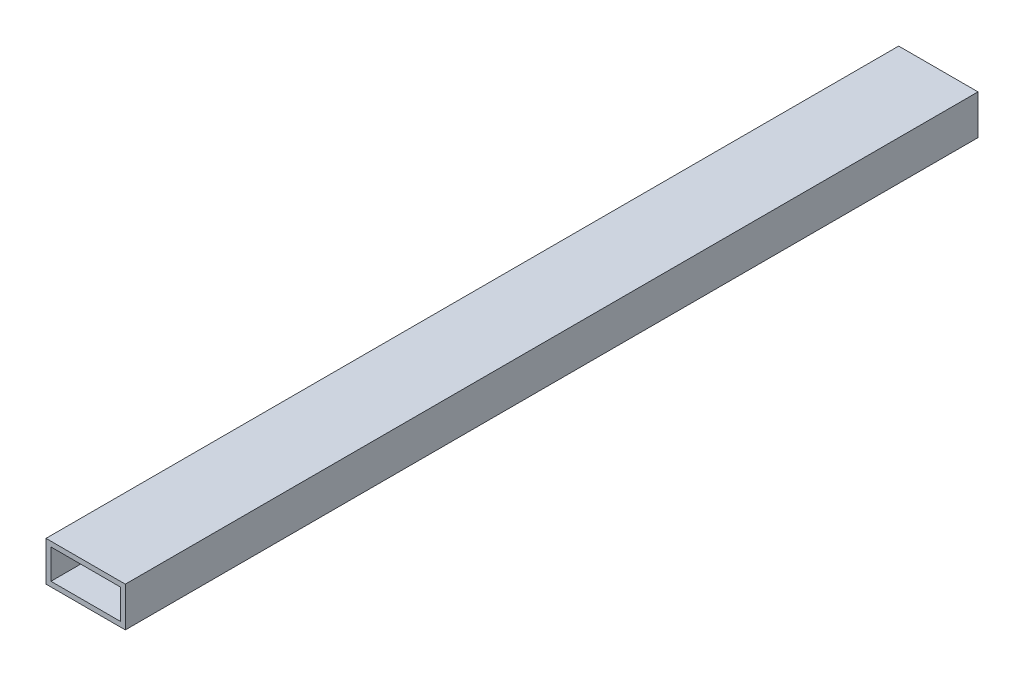
SolidWorks part; units mm, degrees
ref_plane "Front Plane" through (0, 0, 0) normal (0, 0, 1) x (1, 0, 0)
ref_plane "Top Plane" through (0, 0, 0) normal (0, 1, 0) x (1, 0, 0)
ref_plane "Right Plane" through (0, 0, 0) normal (1, 0, 0) x (0, 0, -1)
sketch "Sketch1" plane through (0, 0, 0) normal (0, 0, 1) x (1, 0, 0)
  line L0 (3.175, 22.225) -> (47.625, 22.225)
  line L1 (0, 0) -> (50.8, 0)
  line L2 (0, 0) -> (0, 25.4)
  line L3 (0, 25.4) -> (50.8, 25.4)
  line L4 (50.8, 0) -> (50.8, 25.4)
  line L5 (47.625, 3.175) -> (47.625, 22.225)
  line L6 (3.175, 3.175) -> (47.625, 3.175)
  line L7 (3.175, 3.175) -> (3.175, 22.225)
  dimension "D1" = 25.4
  dimension "D2" = 50.8
  dimension "D3" = 3.175
extrude "Boss-Extrude1" add sketch "Sketch1" along normal blind 546.1
